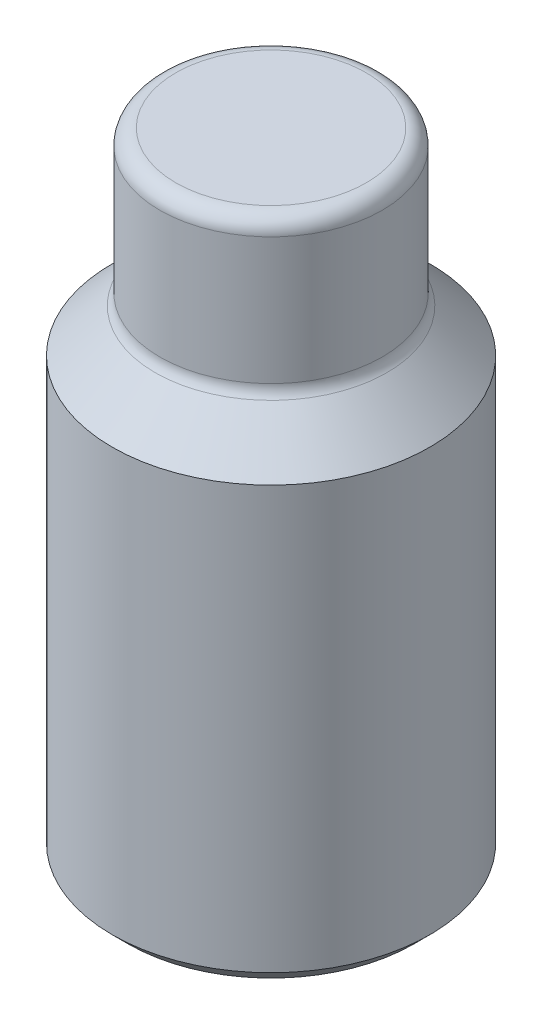
SolidWorks part; units mm, degrees
material "1023 Carbon Steel Sheet (SS)"
ref_plane "Front Plane" through (0, 0, 0) normal (0, 0, 1) x (1, 0, 0)
ref_plane "Top Plane" through (0, 0, 0) normal (0, 1, 0) x (1, 0, 0)
ref_plane "Right Plane" through (0, 0, 0) normal (1, 0, 0) x (0, 0, -1)
sketch "Sketch1" plane through (0, 0, 0) normal (0, 1, 0) x (1, 0, 0)
  circle A0 centre (0, 0) radius 5
  dimension "D1" = 10
extrude "Boss-Extrude1" add sketch "Sketch1" along normal blind 15
sketch "Sketch2" plane through (0, 15, 0) normal (0, 1, 0) x (1, 0, 0)
  circle A0 centre (0, 0) radius 3.5
  dimension "D1" = 7
extrude "Boss-Extrude2" add sketch "Sketch2" along normal blind 5
fillet "Fillet1" radius 0.5 2 edges at (0, 15, 3.5) (0, 20, 3.5)
sketch "Sketch3" plane through (0, 0, 0) normal (0, 0, 1) x (1, 0, 0)
  line L0 (-5, 13.7929) -> (-3.6464, 15.1464)
  line L1 (-5, 15) -> (-5, 0) construction
  line L3 (5, 15) -> (-5, 15) construction
  line L4 (-5, 15) -> (-5, 13.7929)
  line L5 (-5, 15) -> (-3.6464, 15.1464)
  arc A0 (-4, 15) -> (-3.5, 15.5) centre (-4, 15.5) ccw construction
  arc A1 (-4, 15) -> (-3.5, 15.5) centre (-4, 15.5) ccw construction
  dimension "D1" = 45
revolve "Cut-Revolve1" cut sketch "Sketch3" angle 360 about axis through (0, 20, 0) along (0, -1, 0)
hole_wizard "Ø5.0mm Dowel Hole2" positions "Sketch5" profile "Sketch6" hole size "Ø5.0" standard "ISO"
sketch "Sketch5" plane through (0, 0, 0) normal (0, -1, 0) x (-1, 0, 0)
  point P0 (0, 0)
sketch "Sketch6" plane through (0, 0, 0) normal (1, 0, 0) x (0, 0, -1)
  line L0 (0, 0) -> (0, 7.5022)
  line L1 (0, 7.5022) -> (2.5, 6)
  line L2 (2.5, 6) -> (2.5, 0)
  line L5 (2.5, 0) -> (0, 0)
  line L10 (0, 7.5022) -> (-2.5, 6) construction
  line L11 (0, -6.35) -> (0, 107.95) construction
  dimension "Hole Dia." = 5
  dimension "Hole Depth" = 6
  dimension "Drill Angle" = 118
sketch "Sketch4" plane through (0, 0, 0) normal (0, -1, 0) x (1, 0, 0)
  line L1 (2.8868, 0) -> (1.4434, 2.5)
  line L2 (1.4434, 2.5) -> (-1.4434, 2.5)
  line L3 (-1.4434, 2.5) -> (-2.8868, 0)
  line L4 (-2.8868, 0) -> (-1.4434, -2.5)
  line L5 (-1.4434, -2.5) -> (1.4434, -2.5)
  line L6 (1.4434, -2.5) -> (2.8868, 0)
  circle A0 centre (0, 0) radius 2.5 construction
  dimension "D1" = 5
extrude "Cut-Extrude1" cut sketch "Sketch4" against normal blind 6 contours L3 L4 L5 L6 L1 L2
chamfer "Chamfer1" distance 0.5 angle 45 1 edges at (0, 0, 5)
